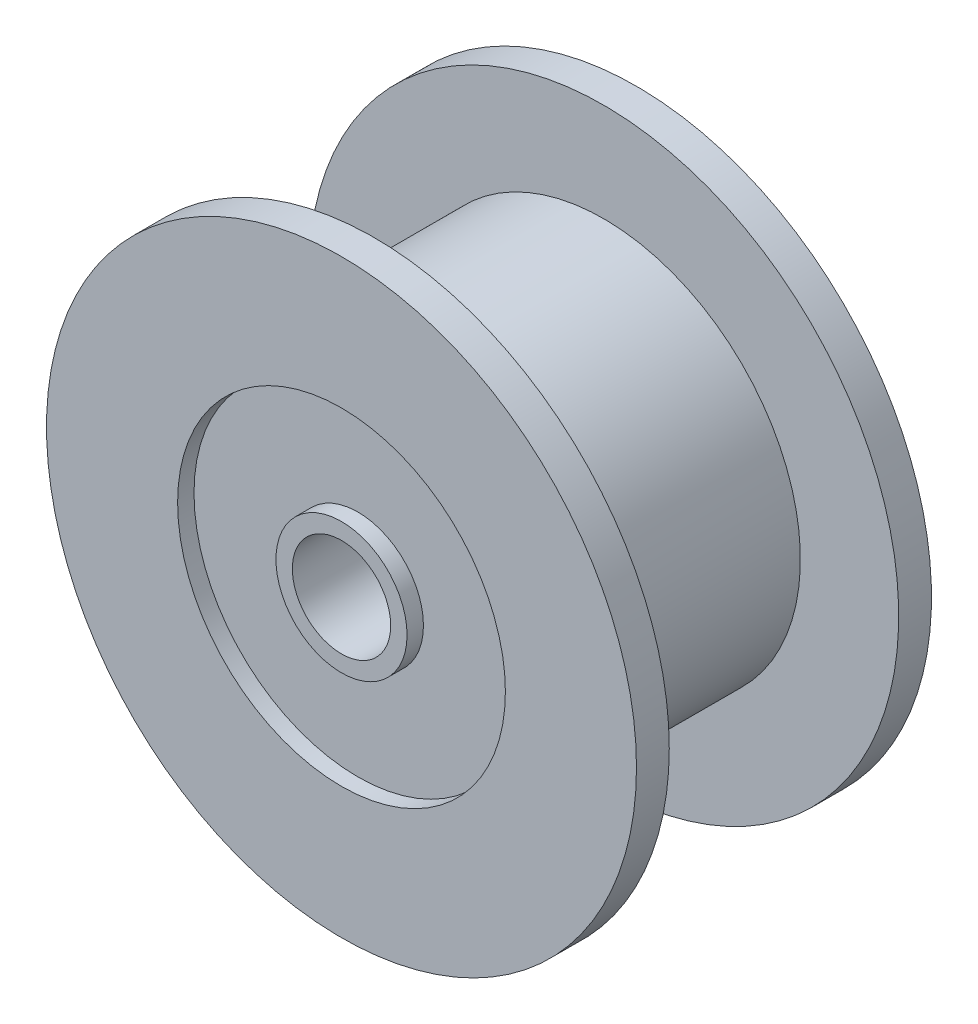
SolidWorks part; units mm, degrees
ref_plane "前视基准面" through (0, 0, 0) normal (0, 0, 1) x (1, 0, 0)
ref_plane "上视基准面" through (0, 0, 0) normal (0, 1, 0) x (1, 0, 0)
ref_plane "右视基准面" through (0, 0, 0) normal (1, 0, 0) x (0, 0, -1)
sketch "草图1" plane through (0, 0, 0) normal (0, 0, 1) x (1, 0, 0)
  circle A0 centre (0, 0) radius 6
extrude "凸台-拉伸1" add sketch "草图1" along normal blind 7
sketch "草图2" plane through (0, 0, 7) normal (0, 0, 1) x (1, 0, 0)
  circle A0 centre (0, 0) radius 9
extrude "凸台-拉伸2" add sketch "草图2" along normal blind 1
sketch "草图3" plane through (0, 0, 0) normal (0, 0, -1) x (-1, 0, 0)
  circle A0 centre (0, 0) radius 9
extrude "凸台-拉伸3" add sketch "草图3" along normal blind 1
sketch "草图4" plane through (0, 0, 8) normal (0, 0, 1) x (1, 0, 0)
  circle A0 centre (0, 0) radius 1.5
extrude "切除-拉伸2" cut sketch "草图4" against normal blind 11
sketch "草图5" plane through (0, 0, -1) normal (0, 0, -1) x (-1, 0, 0)
  circle A0 centre (0, 0) radius 2
  circle A1 centre (0, 0) radius 5
extrude "切除-拉伸3" cut sketch "草图5" against normal blind 0.5
sketch "草图6" plane through (0, 0, 8) normal (0, 0, 1) x (1, 0, 0)
  circle A0 centre (0, 0) radius 2
  circle A1 centre (0, 0) radius 5
extrude "切除-拉伸4" cut sketch "草图6" against normal blind 0.5
equation "\"0。5\"=11"
